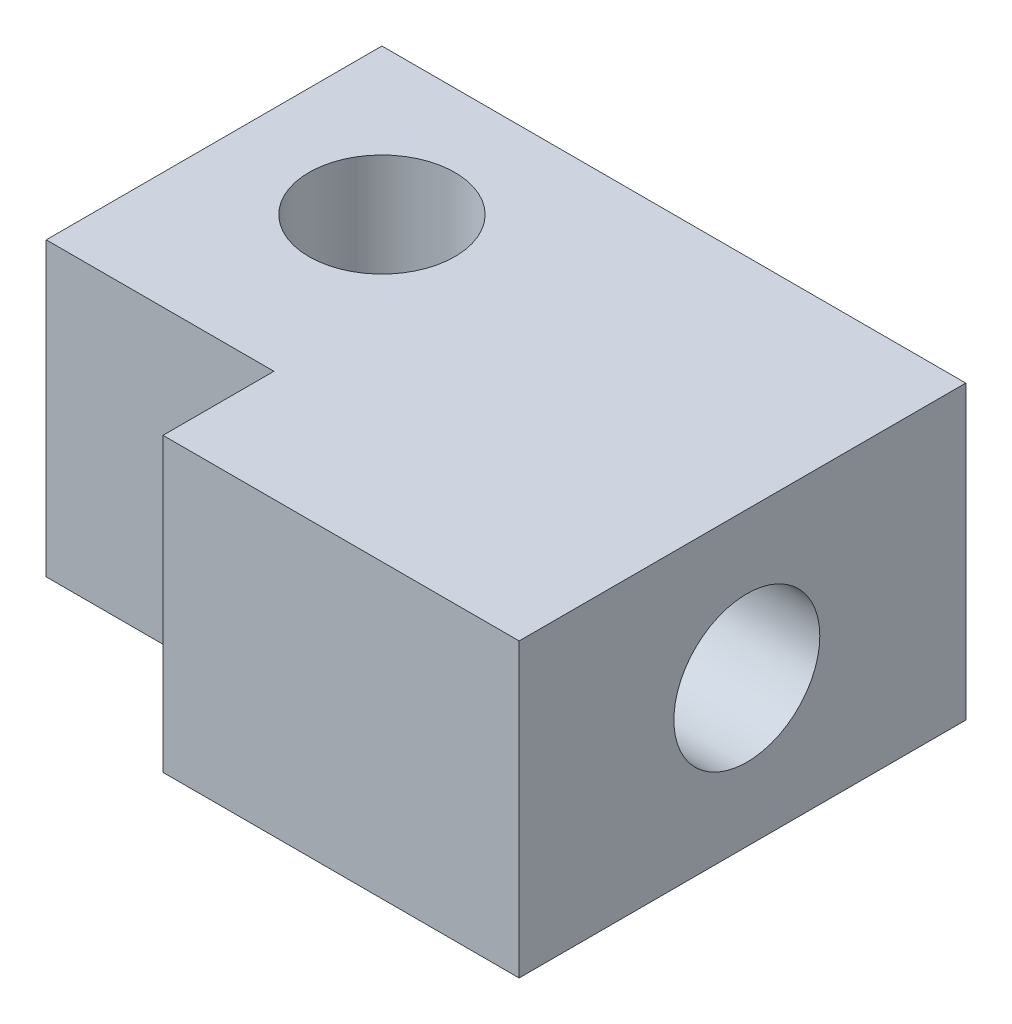
SolidWorks part; units mm, degrees
ref_plane "Front Plane" through (0, 0, 0) normal (0, 0, 1) x (1, 0, 0)
ref_plane "Top Plane" through (0, 0, 0) normal (0, 1, 0) x (1, 0, 0)
ref_plane "Right Plane" through (0, 0, 0) normal (1, 0, 0) x (0, 0, -1)
sketch "Sketch4" plane through (0, 0, 0) normal (0, 1, 0) x (1, 0, 0)
  line L0 (5, -5) -> (5, -86)
  line L5 (5, -86) -> (79, -86)
  line L7 (5, -5) -> (79, -5)
  line L8 (5, -5) -> (79, -5) construction
  line L9 (5, -5) -> (5, -86) construction
  line L10 (-7.25, -5) -> (-7.25, -86)
  line L11 (91.25, -8.9) -> (91.25, -88.5)
  line L12 (79, -5) -> (79, -45.5)
  line L13 (79, -83.5) -> (82.9, -83.5)
  line L14 (82.9, -82.1) -> (82.9, -83.5)
  line L15 (5, -83.5) -> (81.5, -83.5) construction
  line L16 (79, -88.5) -> (91.25, -88.5)
  line L17 (82.9, -82.1) -> (91.25, -82.1)
  line L18 (5, -45.5) -> (79, -45.5)
  line L19 (79, -82.1) -> (91.25, -82.1) construction
  line L20 (79, -83.5) -> (79, -88.5)
  line L21 (79, -2.5) -> (89, -2.5)
  line L22 (79, -7.5) -> (79, -2.5)
  line L23 (79, -83.5) -> (91.25, -83.5) construction
  line L25 (5, -86) -> (81.5, -86) construction
  line L27 (82.9, -10.15) -> (82.9, -8.25)
  line L29 (88.5, -82.1) -> (88.5, -88.5)
  line L31 (89, -2.5) -> (89, -10.15)
  line L32 (82.9, -10.15) -> (89, -10.15)
  line L33 (79, -8.25) -> (82.9, -8.25)
  circle A0 centre (5, -5) radius 1.25
  circle A1 centre (81.5, -5) radius 1.25
  circle A2 centre (81.5, -86) radius 1.25
  circle A3 centre (5, -86) radius 1.25
  point P3 (88.5, -2.5)
  point P4 (82.9, -5)
  point P7 (81.5, -86)
  point P8 (81.5, -5)
  point P27 (82.9, -86)
  point P33 (91.25, -2.5)
  dimension "D1" = 2
  dimension "D4" = 81
  dimension "D5" = 12.25
  dimension "D2" = 2
extrude "Boss-Extrude1" add sketch "Sketch4" along normal blind 5
sketch "Sketch5" plane through (89, 0, 0) normal (1, 0, 0) x (0, 0, -1)
  line L0 (-2.5, 5) -> (-2.5, 0)
  line L1 (-6.25, 5) -> (-6.25, 0)
  circle A0 centre (-6.25, 2.5) radius 1.25
  dimension "D1" = 3.75
extrude "Cut-Extrude1" cut sketch "Sketch5" against normal blind 10 contours L1 A0 | L1 A0
